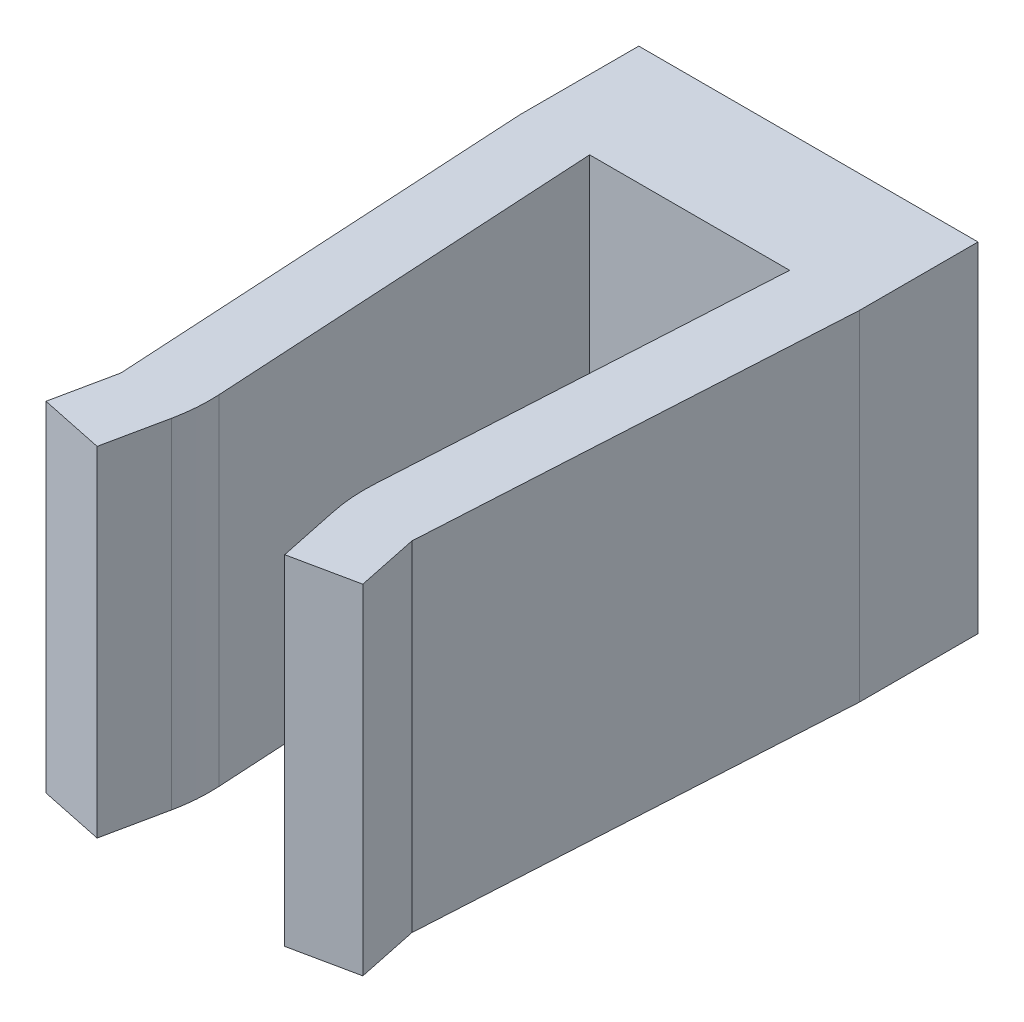
SolidWorks part; units mm, degrees
ref_plane "Front Plane" through (0, 0, 0) normal (0, 0, 1) x (1, 0, 0)
ref_plane "Top Plane" through (0, 0, 0) normal (0, 1, 0) x (1, 0, 0)
ref_plane "Right Plane" through (0, 0, 0) normal (1, 0, 0) x (0, 0, -1)
sketch "Sketch1" plane through (0, 0, 0) normal (0, 0, 1) x (1, 0, 0)
  line L1 (0, 0) -> (20, 0)
  line L2 (0, 0) -> (0, -20)
  line L3 (0, -20) -> (20, -20)
  line L4 (20, 0) -> (20, -20)
  dimension "D1" = 20
  dimension "D2" = 20
extrude "Boss-Extrude1" add sketch "Sketch1" along normal blind 7
sketch "Sketch2" plane through (0, 0, 7) normal (0, 0, 1) x (1, 0, 0)
  line L0 (20, -20) -> (20, 0) construction
  line L1 (20, 0) -> (0, 0) construction
  circle A0 centre (10, -10) radius 2.75
  point P4 (20, -10)
  point P7 (10, 0)
  dimension "D1" = 5.5
extrude "Cut-Extrude1" cut sketch "Sketch2" against normal through all
sketch "Sketch3" plane through (0, 0, 0) normal (0, 1, 0) x (1, 0, 0)
  line L0 (0, -7) -> (1.4231, -31.9595)
  line L1 (1.4231, -31.9595) -> (0.66, -35.607)
  line L2 (0.66, -35.607) -> (4.4702, -36.4041)
  line L3 (4.4702, -36.4041) -> (5.5, -31.4813)
  line L4 (5.5, -31.4813) -> (4.1042, -7)
  line L5 (20, -7) -> (0, -7) construction
  line L6 (4.1042, -7) -> (0, -7)
  line L7 (10, 0) -> (10, -7) construction
  line L8 (20, 0) -> (0, 0) construction
  line L9 (15.8958, -7) -> (20, -7)
  line L10 (14.5, -31.4813) -> (15.8958, -7)
  line L11 (15.5298, -36.4041) -> (14.5, -31.4813)
  line L12 (19.34, -35.607) -> (15.5298, -36.4041)
  line L13 (18.5769, -31.9595) -> (19.34, -35.607)
  line L14 (20, -7) -> (18.5769, -31.9595)
  point P19 (5.5, -31.4813)
  dimension "D1" = 9
  dimension "D2" = 25
extrude "Boss-Extrude2" add sketch "Sketch3" against normal blind 20
fillet "Fillet1" radius 10 2 edges at (14.5, -10, 31.4813) (5.5, -10, 31.4813)
